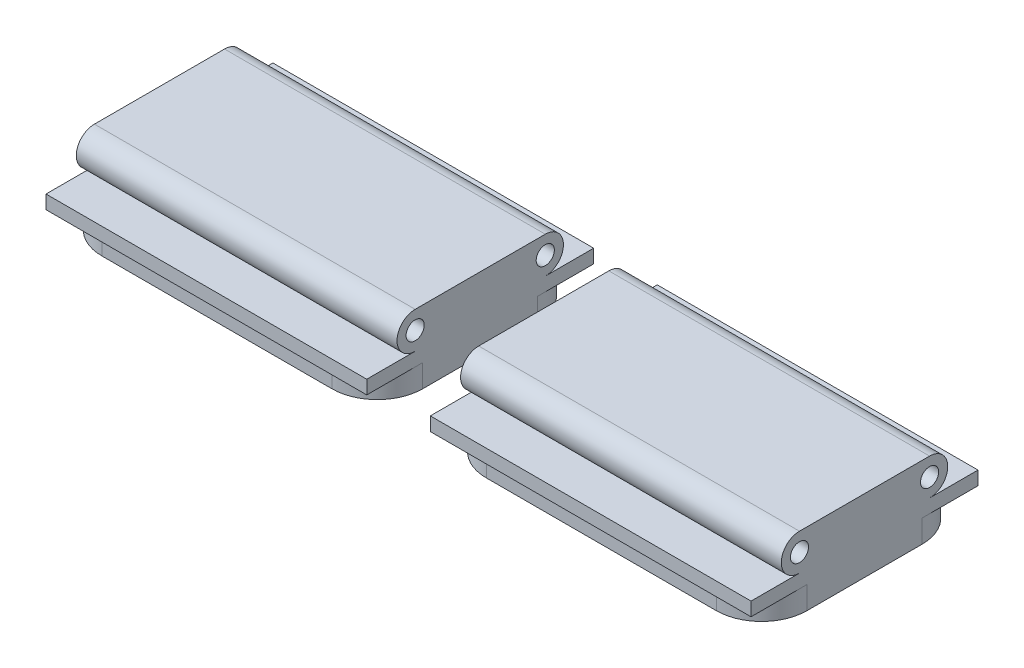
SolidWorks part; units mm, degrees
ref_plane "Ön Düzlem" through (0, 0, 0) normal (0, 0, 1) x (1, 0, 0)
ref_plane "Üst Düzlem" through (0, 0, 0) normal (0, 1, 0) x (1, 0, 0)
ref_plane "Sağ Düzlem" through (0, 0, 0) normal (1, 0, 0) x (0, 0, -1)
sketch "Çizim1" plane through (0, 0, 0) normal (1, 0, 0) x (0, 0, -1)
  line L0 (-43, 0) -> (43, 0) construction
  line L1 (-43, 0) -> (43, 0) construction
  line L2 (-43, 12) -> (43, 12)
  line L3 (-43, -12) -> (43, -12)
  line L4 (43, -12) -> (75, -12)
  line L5 (75, -12) -> (75, -21)
  line L6 (75, -21) -> (68, -21)
  line L7 (68, -21) -> (68, -36)
  line L8 (68, -36) -> (-68, -36)
  line L9 (0, 0) -> (0, -59.3674) construction
  line L10 (-43, -12) -> (-75, -12)
  line L11 (-75, -12) -> (-75, -21)
  line L12 (-75, -21) -> (-68, -21)
  line L13 (-68, -21) -> (-68, -36)
  arc A0 (-43, 12) -> (-43, -12) centre (-43, 0) ccw
  arc A1 (43, -12) -> (43, 12) centre (43, 0) ccw
  circle A2 centre (-43, 0) radius 6
  circle A3 centre (43, 0) radius 6
  point P4 (0, 0)
  point P6 (0, 0)
  point P26 (0, -36)
  dimension "D3" = 12
  dimension "D4" = 12
  dimension "D1" = 86
  dimension "D2" = 24
  dimension "D5" = 9
  dimension "D6" = 15
  dimension "D7" = 75
  dimension "D8" = 68
extrude "Yükseklik-Ekstrüzyon1" add sketch "Çizim1" along normal mid plane 212 contours L3 A1 L2 A0 A3 A2 | L12 L13 L8 L7 L6 L5 L4 L3 L10 L11
fillet "Radyus1" radius 30 4 edges at (-106, -28.5, -68) (106, -28.5, -68) (106, -28.5, 68) (-106, -28.5, 68)
ref_plane "Düzlem1" through (-127, 0, 0) normal (-1, 0, 0) x (0, 0, 1)
mirror "Aynalama16" about plane through (-127, 0, 0) normal (-1, 0, 0) of bodies 101
